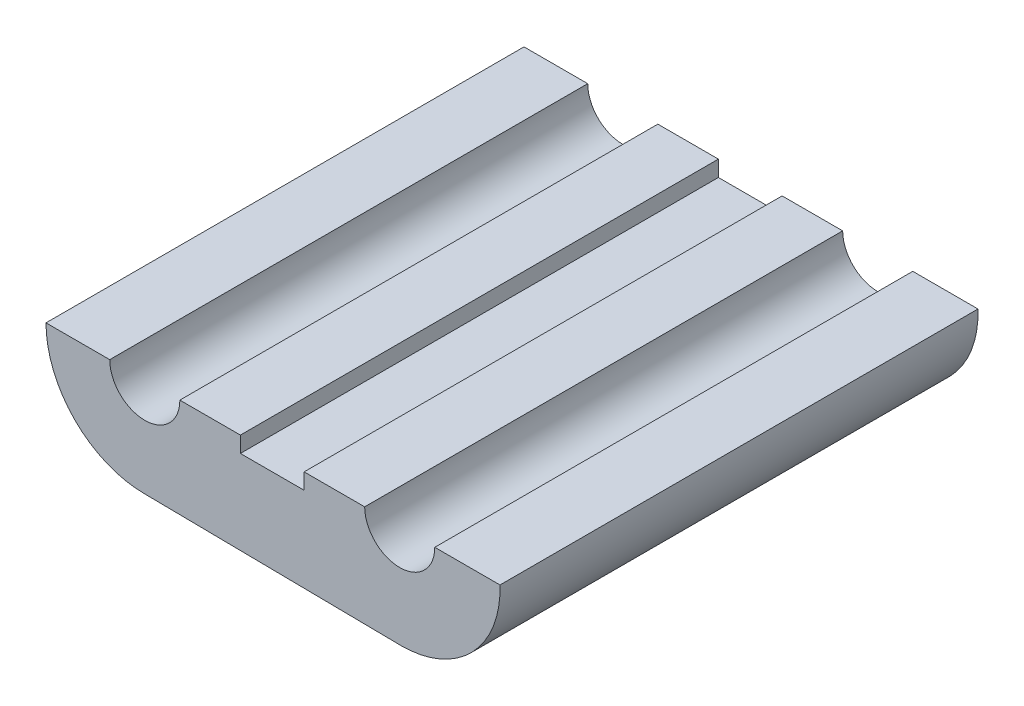
SolidWorks part; units mm, degrees
ref_plane "Front Plane" through (0, 0, 0) normal (0, 0, 1) x (1, 0, 0)
ref_plane "Top Plane" through (0, 0, 0) normal (0, 1, 0) x (1, 0, 0)
ref_plane "Right Plane" through (0, 0, 0) normal (1, 0, 0) x (0, 0, -1)
sketch "Sketch1" plane through (0, 0, 0) normal (0, 0, 1) x (1, 0, 0)
  line L0 (-1.6124, 5.0197) -> (-5.3402, 2.6003)
  line L1 (-3.6526, -3.1) -> (4.396, -3.2018)
  line L3 (2.3464, 4.994) -> (6.1173, 2.4763)
  circle A0 centre (-3.6526, 0) radius 1.1
  circle A1 centre (4.3474, 0) radius 1.1
  arc A2 (-3.0961, 3.0497) -> (-0.879, -1.3847) centre (-3.6526, 0) ccw
  circle A4 centre (0.3474, 2) radius 1.6
  arc A5 (-0.879, -1.3847) -> (1.5739, -1.3847) centre (0.3474, 2) ccw
  circle A6 centre (-3.6526, 0) radius 3.1 construction
  arc A9 (1.5739, -1.3847) -> (3.8214, 2.9444) centre (4.396, -0.1018) ccw
  circle A10 centre (0.3474, 2) radius 3.6 construction
  arc A12 (3.8214, 2.9444) -> (-3.0961, 3.0497) centre (0.3474, 2) ccw
  dimension "D1" = 2.2
  dimension "D2" = 2.2
  dimension "D5" = 3.2
  dimension "D3" = 8
  dimension "D6" = 2
  dimension "D4" = 2
  dimension "D7" = 2
extrude "Boss-Extrude1" add sketch "Sketch1" along normal blind 15 contours A9 A5 A2 L1 | A9 A12 A2 A5 L1 A0 A1 A4 | A12 A9 L3 | A12 L0 A2
sketch "Sketch3" plane through (0, 0, 15) normal (0, 0, 1) x (1, 0, 0)
  line L1 (-3.6526, 0) -> (12.6552, 0)
  line L2 (-3.6526, 0) -> (-3.6526, -4.7746)
  line L3 (-3.6526, -4.7746) -> (12.6552, -4.7746)
  line L4 (12.6552, 0) -> (12.6552, -4.7746)
  line L5 (-3.6526, 0) -> (-12.2596, 0)
  line L6 (-3.6526, 0) -> (-3.6526, -4.7746)
  line L7 (-3.6526, -4.7746) -> (-12.2596, -4.7746)
  line L8 (-12.2596, 0) -> (-12.2596, -4.7746)
  arc M2 (4.396, -3.2018) -> (6.1173, 2.4763) centre (4.396, -0.1018) ccw
  line M3 (6.1173, 2.4763) -> (2.3464, 4.994)
  arc M4 (2.3464, 4.994) -> (-1.6124, 5.0197) centre (0.3474, 2) ccw
  line M5 (-1.6124, 5.0197) -> (-5.3402, 2.6003)
  arc M6 (-5.3402, 2.6003) -> (-3.6526, -3.1) centre (-3.6526, 0) ccw
  circle M7 centre (-3.6526, 0) radius 1.1
  circle M8 centre (4.3474, 0) radius 1.1
  circle M9 centre (0.3474, 2) radius 1.6
extrude "Cut-Extrude1" cut sketch "Sketch3" against normal blind 15 contours L5 L1 M7 M8 M2 M3 M4 M5 M6 M9
sketch "Sketch5" plane through (0, 0, 15) normal (0, 0, 1) x (1, 0, 0)
  line L0 (-2.5526, 0) -> (3.2474, 0) construction
  line L1 (-0.6526, 0) -> (1.3474, 0)
  line L2 (-0.6526, 0) -> (-0.6526, -0.5)
  line L3 (-0.6526, -0.5) -> (1.3474, -0.5)
  line L4 (1.3474, 0) -> (1.3474, -0.5)
  line L5 (-0.6526, 0) -> (1.3474, -0.5) construction
  line L6 (-0.6526, -0.5) -> (1.3474, 0) construction
  point P0 (0.3474, -0.25)
  point P7 (0.3474, -0.25)
  dimension "D1" = 0.5
  dimension "D2" = 2
extrude "Cut-Extrude2" cut sketch "Sketch5" against normal through all
